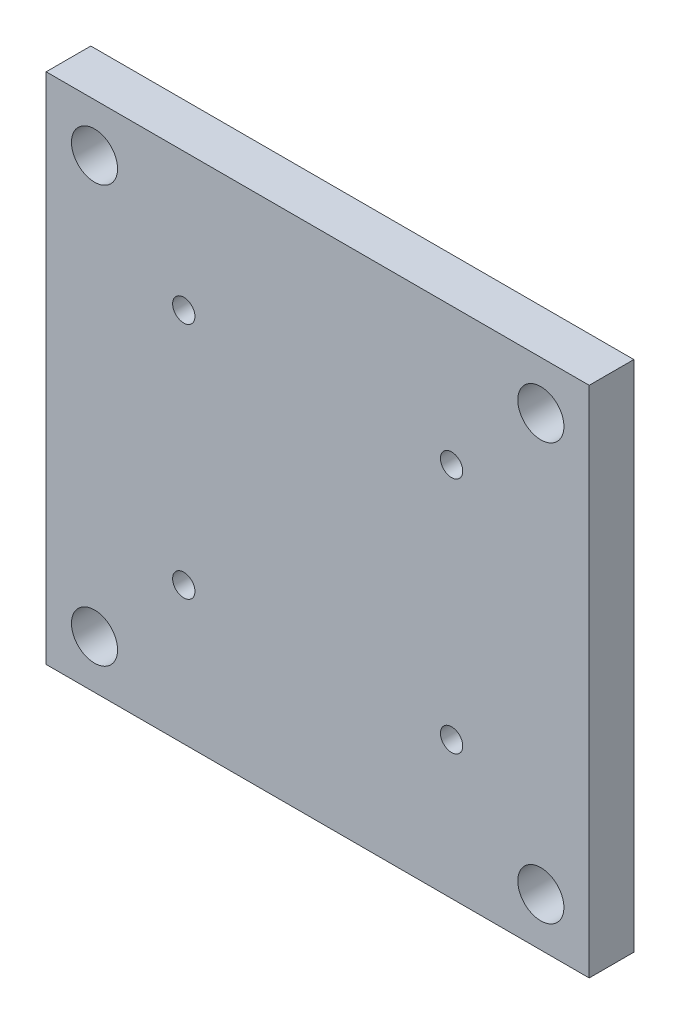
SolidWorks part; units mm, degrees
ref_plane "Alzado" through (0, 0, 0) normal (0, 0, 1) x (1, 0, 0)
ref_plane "Planta" through (0, 0, 0) normal (0, 1, 0) x (1, 0, 0)
ref_plane "Vista lateral" through (0, 0, 0) normal (1, 0, 0) x (0, 0, -1)
sketch "Croquis1" plane through (0, 0, 0) normal (0, 0, 1) x (1, 0, 0)
  line L1 (0, 0) -> (73, 0)
  line L2 (0, 0) -> (0, 69)
  line L3 (0, 69) -> (73, 69)
  line L4 (73, 0) -> (73, 69)
  circle A0 centre (6.5, 6.5) radius 3.1
  circle A1 centre (66.5, 6.5) radius 3.1
  circle A2 centre (66.5, 62.5) radius 3.1
  circle A3 centre (6.5, 62.5) radius 3.1
  circle A4 centre (18.5, 50.5) radius 1.5
  circle A5 centre (54.5, 50.5) radius 1.5
  circle A6 centre (54.5, 18.5) radius 1.5
  circle A7 centre (18.5, 18.5) radius 1.5
  dimension "D3" = 6.5
  dimension "D4" = 6.5
  dimension "D5" = 6.5
  dimension "D6" = 6.5
  dimension "D7" = 6.2
  dimension "D8" = 3
  dimension "D9" = 3
  dimension "D10" = 3
  dimension "D11" = 3
  dimension "D13" = 18.5
  dimension "D14" = 36
  dimension "D15" = 32
  dimension "D16" = 32
  dimension "D17" = 36
  dimension "D18" = 60
  dimension "D19" = 56
  dimension "D1" = 69
  dimension "D2" = 73
  dimension "D12" = 18.5
extrude "Saliente-Extruir1" add sketch "Croquis1" along normal blind 6
sketch "Croquis2" plane through (0, 0, 0) normal (0, 0, -1) x (-1, 0, 0)
  circle A0 centre (-54.5, 50.5) radius 2.75
  circle A1 centre (-18.5, 50.5) radius 2.75
  circle A2 centre (-18.5, 18.5) radius 2.75
  circle A3 centre (-54.5, 18.5) radius 2.75
extrude "Cortar-Extruir1" cut sketch "Croquis2" against normal blind 3
